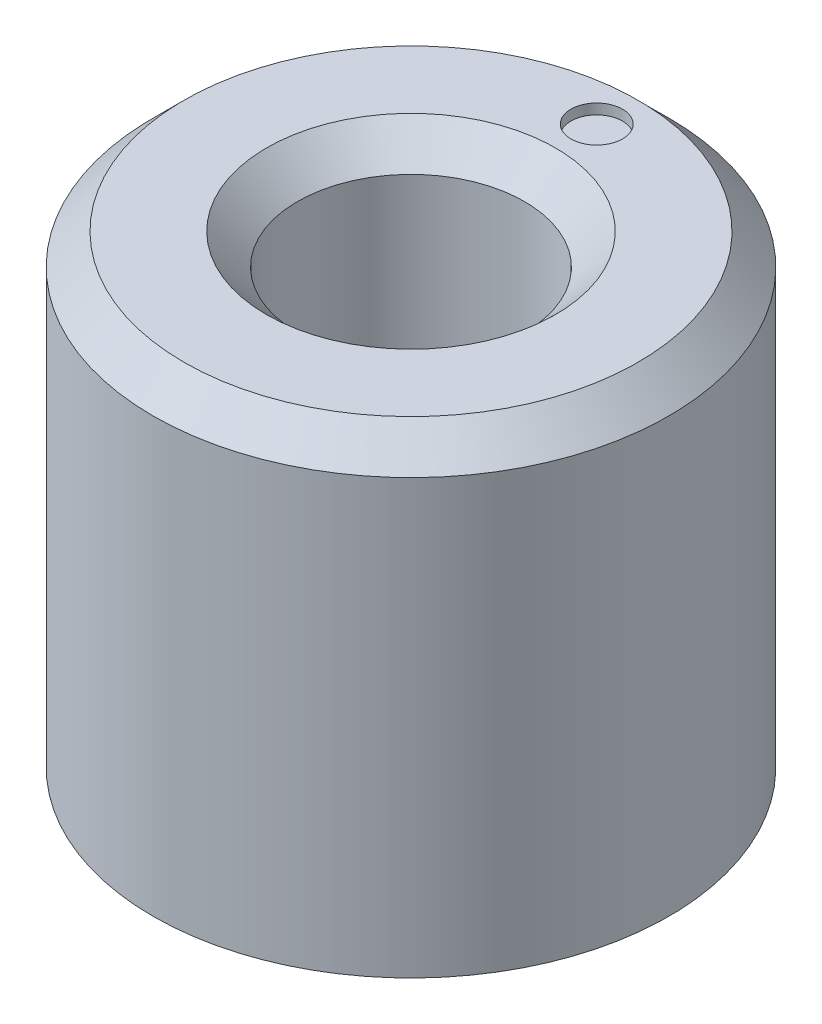
SolidWorks part; units mm, degrees
ref_plane "正面" through (0, 0, 0) normal (0, 0, 1) x (1, 0, 0)
ref_plane "平面" through (0, 0, 0) normal (0, 1, 0) x (1, 0, 0)
ref_plane "右側面" through (0, 0, 0) normal (1, 0, 0) x (0, 0, -1)
sketch "ｽｹｯﾁ1" plane through (0, 0, 0) normal (0, 1, 0) x (1, 0, 0)
  circle A0 centre (0, 0) radius 5
  dimension "D1" = 10
extrude "ﾎﾞｽ - 押し出し1" add sketch "ｽｹｯﾁ1" along normal blind 9
sketch "ｽｹｯﾁ2" plane through (0, 0, 0) normal (0, 1, 0) x (1, 0, 0)
  circle A0 centre (0, 0) radius 2.2
  circle A1 centre (0, 0) radius 5 construction
  dimension "D1" = 2.8
extrude "ｶｯﾄ - 押し出し1" cut sketch "ｽｹｯﾁ2" along normal through all
sketch "ｽｹｯﾁ3" plane through (0, 9, 0) normal (0, 1, 0) x (1, 0, 0)
  line L0 (0, 2.2) -> (0, 5) construction
  circle A0 centre (0, 3.6) radius 0.5
  circle A1 centre (0, 0) radius 2.2 construction
  circle A2 centre (0, 0) radius 5 construction
  point P10 (0, 3.6)
  dimension "D1" = 1
extrude "ｶｯﾄ - 押し出し2" cut sketch "ｽｹｯﾁ3" against normal blind 0.2 contours A0
chamfer "面取り1" distance 0.6 angle 45 2 edges at (0, 9, 2.2) (0, 9, 5)
